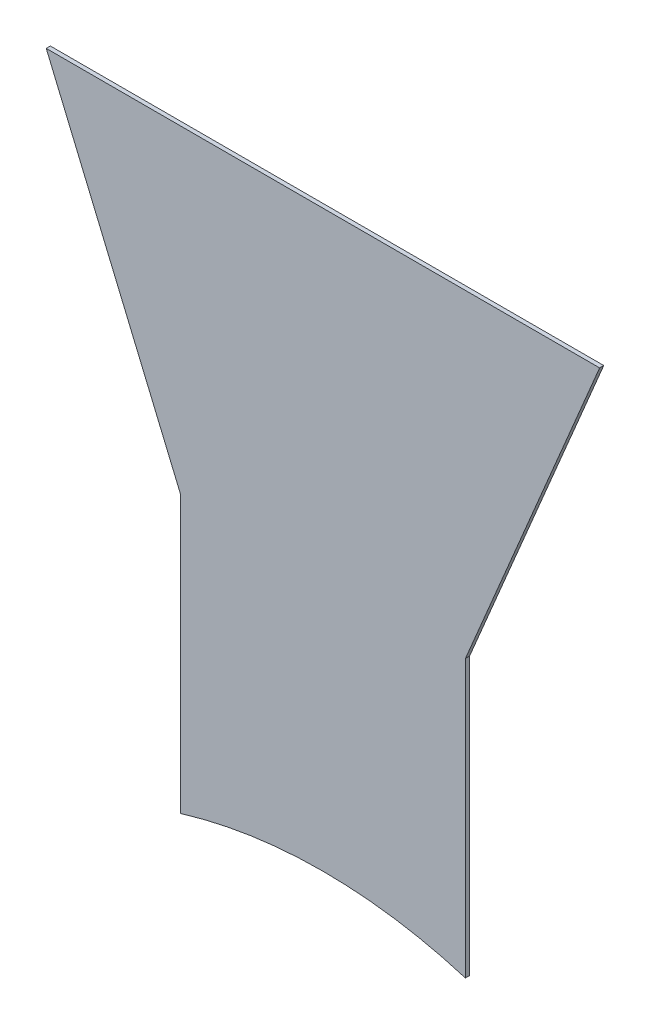
SolidWorks part; units mm, degrees
material "Plain Carbon Steel"
ref_plane "Front Plane" through (0, 0, 0) normal (0, 0, 1) x (1, 0, 0)
ref_plane "Top Plane" through (0, 0, 0) normal (0, 1, 0) x (1, 0, 0)
ref_plane "Right Plane" through (0, 0, 0) normal (1, 0, 0) x (0, 0, -1)
sketch "Sketch1" plane through (0, 0, 0) normal (0, 0, 1) x (1, 0, 0)
  line L0 (-52.3189, 171.5168) -> (-52.3189, 273.1168)
  line L5 (-52.3189, 0) -> (52.3189, 0) construction
  line L8 (101.6, 390.1654) -> (52.3189, 273.1168)
  line L9 (52.3189, 0) -> (52.3189, 171.5168) construction
  line L10 (-52.3189, 0) -> (-52.3189, 171.5168) construction
  line L11 (-101.6, 390.1654) -> (-52.3189, 273.1168)
  line L12 (52.3189, 171.5168) -> (52.3189, 273.1168)
  line L13 (-101.6, 390.1654) -> (101.6, 390.1654)
  line L14 (0, 390.1654) -> (0, 0) construction
  circle A0 centre (0, 0) radius 179.3189 construction
  arc A1 (52.3189, 171.5168) -> (-52.3189, 171.5168) centre (0, 0) ccw
  point P11 (0, 0)
  dimension "D1" = 358.6378
  dimension "D2" = 101.6
  dimension "D3" = 127
  dimension "D4" = 203.2
  dimension "D5" = 104.6378
extrude "Boss-Extrude1" add sketch "Sketch1" along normal blind 1.5189
